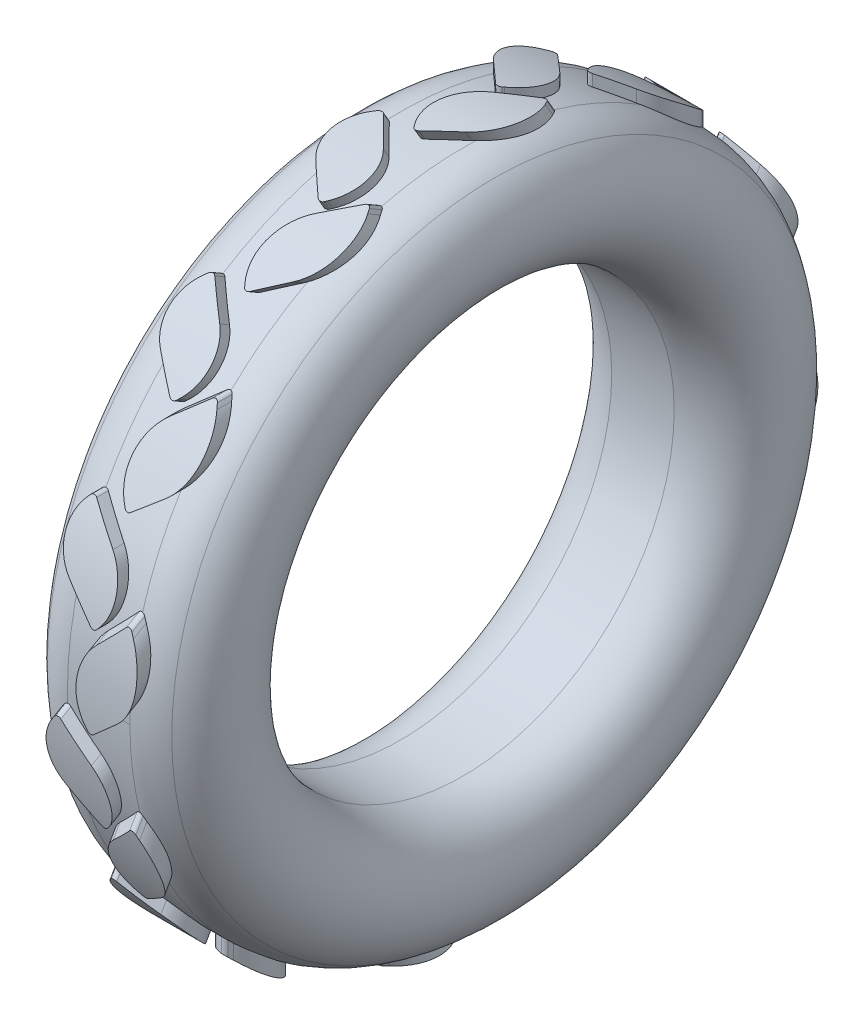
SolidWorks part; units mm, degrees
ref_plane "Front Plane" through (0, 0, 0) normal (0, 0, 1) x (1, 0, 0)
ref_plane "Top Plane" through (0, 0, 0) normal (0, 1, 0) x (1, 0, 0)
ref_plane "Right Plane" through (0, 0, 0) normal (1, 0, 0) x (0, 0, -1)
sketch "Sketch1" plane through (0, 0, 0) normal (0, 0, 1) x (1, 0, 0)
  line L0 (-7.5, 80) -> (7.5, 80)
  line L1 (7.5, 50.7647) -> (-7.5, 50.7647)
  line L12 (0, 0) -> (57.2495, 0) construction
  arc A0 (14.9518, 77.4059) -> (7.5, 50.7647) centre (5.637, 65.6485) cw
  arc A1 (-14.9518, 77.4059) -> (-7.5, 50.7647) centre (-5.637, 65.6485) ccw
  arc A2 (7.5, 80) -> (14.9518, 77.4059) centre (7.5, 68) cw
  arc A3 (-7.5, 80) -> (-14.9518, 77.4059) centre (-7.5, 68) ccw
  point P3 (0, 80)
  point P7 (0, 0)
  point P10 (10, 80)
  point P13 (-10, 80)
  point P14 (0, 0)
  point P15 (0, 0)
  point P16 (0, 0)
  dimension "D1" = 15
  dimension "D4" = 12
  dimension "D2" = 15
  dimension "D6" = 15
  dimension "D3" = 20
  dimension "D5" = 80
ref_plane "Plane1" through (0, 82, 0) normal (0, 1, 0) x (1, 0, 0)
revolve "Revolve2" add sketch "Sketch1" angle 360 about L12
sketch "Sketch3" plane through (0, 82, 0) normal (0, 1, 0) x (1, 0, 0)
  line L0 (-1.1013, 16.4635) -> (-7.7651, 22.6069)
  line L1 (0.327, 16.5379) -> (0.6427, 16.8963)
  line L2 (-8.4918, 36.5682) -> (-8.1761, 36.9266)
  line L3 (-0.084, 30.8576) -> (-6.7478, 37.001)
  line L4 (-14.9518, -77.4059) -> (-14.9518, 77.4059) construction
  line L5 (-7.5, -80) -> (-7.5, 80) construction
  line L6 (1.0848, 37.6094) -> (6.9912, 42.1918)
  line L7 (-0.3137, 37.7805) -> (-0.9152, 38.5439)
  line L8 (8.7158, 56.282) -> (8.1143, 57.0453)
  line L9 (0.8094, 52.634) -> (6.7158, 57.2165)
  line L10 (14.9518, -77.4059) -> (14.9518, 77.4059) construction
  line L11 (7.5, -80) -> (7.5, 80) construction
  arc A0 (-7.7651, 22.6069) -> (-8.4918, 36.5682) centre (-0.987, 29.9593) cw
  arc A1 (0.6427, 16.8963) -> (-0.084, 30.8576) centre (-6.8621, 23.5052) ccw
  arc A2 (0.327, 16.5379) -> (-1.1013, 16.4635) centre (-0.4234, 17.1988) cw
  arc A3 (-8.1761, 36.9266) -> (-6.7478, 37.001) centre (-7.4256, 36.2657) cw
  arc A4 (6.9912, 42.1918) -> (8.7158, 56.282) centre (0.8613, 50.0927) ccw
  arc A5 (-0.9152, 38.5439) -> (0.8094, 52.634) centre (6.9393, 44.7331) cw
  arc A6 (-0.3137, 37.7805) -> (1.0848, 37.6094) centre (0.4718, 38.3995) ccw
  arc A7 (8.1143, 57.0453) -> (6.7158, 57.2165) centre (7.3288, 56.4264) ccw
  point P10 (-14.9518, 29.2324)
  point P17 (-7.5, 37.6944)
  point P28 (14.9518, 48.3681)
  point P35 (7.5, 57.8249)
  dimension "D1" = 10
  dimension "D2" = 1
  dimension "D3" = 10
  dimension "D4" = 1
extrude "Boss-Extrude2" add sketch "Sketch3" against normal up to body
sketch "Sketch4" plane through (0, 0, 0) normal (1, 0, 0) x (0, 0, -1)
  line L0 (16.1988, 82) -> (16.1988, 78.3428) construction
  line L1 (16.1988, 82) -> (16.1988, 80.8941)
  line L2 (57.4264, 55.6975) -> (57.4264, 82) construction
  line L3 (57.4264, 59.2323) -> (57.4264, 82)
  arc A0 (57.4264, 59.2323) -> (16.1988, 80.8941) centre (0, 0) ccw
  spline S0 degree 3 poles (16.1988, 82) (15.4886, 83.7294) (19.7694, 84.5236) (32.7077, 86.8912) (47.6673, 94.197) (57.4264, 82) knots 0 0 0 0 0.106935 0.195115 1 1 1 1
  dimension "D1" = 165
extrude "Cut-Extrude1" cut sketch "Sketch4" against normal through all both and the other way through all
pattern_circular "CirPattern2" count 12 over 360 about axis through (0, 0, 0) along (1, 0, 0) of "Boss-Extrude2", "Cut-Extrude1"
